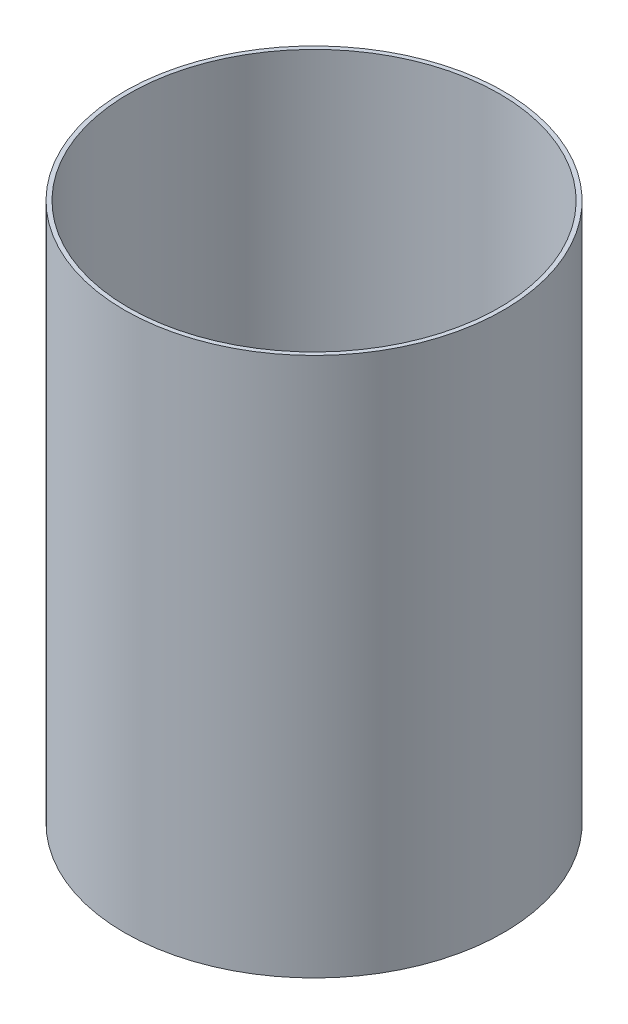
SolidWorks part; units mm, degrees
material "Hexcel AS4C (3000 Filaments)"
ref_plane "Front Plane" through (0, 0, 0) normal (0, 0, 1) x (1, 0, 0)
ref_plane "Top Plane" through (0, 0, 0) normal (0, 1, 0) x (1, 0, 0)
ref_plane "Right Plane" through (0, 0, 0) normal (1, 0, 0) x (0, 0, -1)
sketch "Sketch5" plane through (0, 0, 0) normal (0, 1, 0) x (1, 0, 0)
  circle A0 centre (0, 0) radius 139.7
  circle A1 centre (0, 0) radius 142.875
  dimension "D1" = 279.4
  dimension "D2" = 285.75
extrude "Boss-Extrude1" add sketch "Sketch5" along normal blind 406.4
